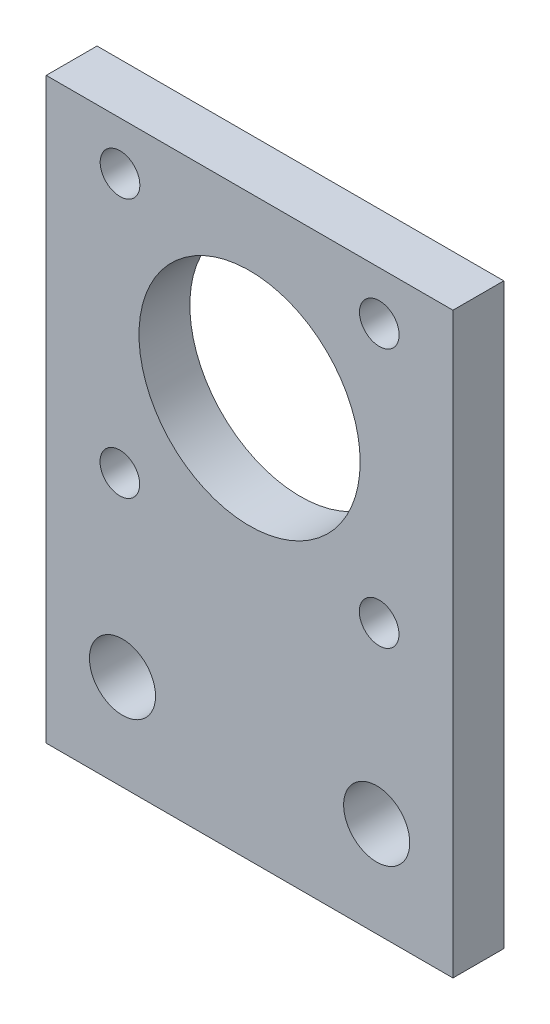
SolidWorks part; units mm, degrees
ref_plane "Front Plane" through (0, 0, 0) normal (0, 0, 1) x (1, 0, 0)
ref_plane "Top Plane" through (0, 0, 0) normal (0, 1, 0) x (1, 0, 0)
ref_plane "Right Plane" through (0, 0, 0) normal (1, 0, 0) x (0, 0, -1)
sketch "Sketch1" plane through (0, 0, 0) normal (0, 0, 1) x (1, 0, 0)
  line L1 (-14.8516, 28.4998) -> (25.7884, 28.4998)
  line L2 (-14.8516, 28.4998) -> (-14.8516, -29.2852)
  line L3 (-14.8516, -29.2852) -> (25.7884, -29.2852)
  line L4 (25.7884, 28.4998) -> (25.7884, -29.2852)
  line L5 (-14.8516, -10.2352) -> (25.7884, -10.2352)
  line L6 (-14.8516, -10.2352) -> (-14.8516, -29.2852)
  line L7 (-14.8516, -29.2852) -> (25.7884, -29.2852)
  line L8 (25.7884, -10.2352) -> (25.7884, -29.2852)
  circle A0 centre (5.4684, 10.7198) radius 11.049
  circle A1 centre (18.1684, -19.7602) radius 3.302
  circle A2 centre (-7.2316, -19.7602) radius 3.302
  circle A3 centre (18.4136, -2.243) radius 1.9812
  circle A4 centre (-7.4944, -2.2254) radius 1.9812
  circle A5 centre (-7.4768, 23.6826) radius 1.9812
  circle A6 centre (18.4312, 23.665) radius 1.9812
  dimension "D5" = 22.098
  dimension "D10" = 6.604
  dimension "D11" = 6.604
  dimension "D22" = 3.9624
  dimension "D23" = 3.9624
  dimension "D24" = 3.9624
  dimension "D25" = 3.9624
  dimension "D1" = 57.785
  dimension "D2" = 40.64
  dimension "D3" = 0
  dimension "D4" = 19.05
  dimension "D6" = 20.32
  dimension "D7" = 17.78
  dimension "D8" = 7.62
  dimension "D9" = 7.62
  dimension "D12" = 9.525
  dimension "D13" = 9.525
  dimension "D14" = 25.908
  dimension "D15" = 25.908
  dimension "D16" = 25.908
  dimension "D17" = 25.908
  dimension "D18" = 18.3197
  dimension "D19" = 18.3197
  dimension "D20" = 18.3197
  dimension "D21" = 18.3197
extrude "Boss-Extrude1" add sketch "Sketch1" along normal blind 5.08 contours L5 L2 L3 L4 A2 A1 | L2 L5 L4 L1 A6 A5 A4 A3 A0
